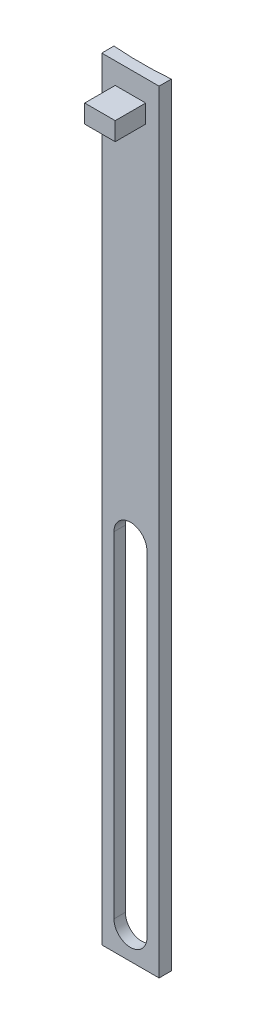
SolidWorks part; units mm, degrees
ref_plane "Front Plane" through (0, 0, 0) normal (0, 0, 1) x (1, 0, 0)
ref_plane "Top Plane" through (0, 0, 0) normal (0, 1, 0) x (1, 0, 0)
ref_plane "Right Plane" through (0, 0, 0) normal (1, 0, 0) x (0, 0, -1)
sketch "Sketch1" plane through (0, 0, 0) normal (0, 0, 1) x (1, 0, 0)
  line L0 (-2.7, -32.5) -> (-2.7, -87.5)
  line L1 (2.7, 32.5) -> (-2.7, 32.5)
  line L2 (2.7, 32.5) -> (2.7, -32.5)
  line L4 (-2.7, 32.5) -> (-2.7, -32.5)
  line L5 (2.7, 32.5) -> (-2.7, -32.5) construction
  line L6 (2.7, -32.5) -> (-2.7, 32.5) construction
  line L7 (-4.7, -32.5) -> (-4.7, 34.5)
  line L8 (-4.7, 34.5) -> (4.7, 34.5)
  line L9 (4.7, 34.5) -> (4.7, -32.5)
  line L10 (2.7, -87.5) -> (2.7, -32.5)
  line L11 (0, 29.2386) -> (0, -29.2386) construction
  line L12 (-4.7, -32.5) -> (-4.7, -92.2)
  line L13 (-4.7, -92.2) -> (4.7, -92.2)
  line L14 (4.7, -32.5) -> (4.7, -92.2)
  arc A2 (-2.7, -32.5) -> (2.7, -32.5) centre (0, -32.5) cw
  arc A3 (-2.7, -87.5) -> (2.7, -87.5) centre (0, -87.5) ccw
  point P0 (0, 0)
  point P13 (0, 0)
  point P19 (-2.7, -53.2591)
  point P20 (0, -90.2)
  dimension "D1" = 2.7
  dimension "D6" = 2
  dimension "D3" = 2
  dimension "D2" = 65
  dimension "D4" = 2
  dimension "D5" = 55
extrude "Boss-Extrude1" add sketch "Sketch1" along normal mid plane 2
sketch "Sketch2" plane through (0, 0, 0) normal (0, 1, 0) x (1, 0, 0)
  line L4 (4.7, 1) -> (-4.7, 1)
  line L5 (-4.7, 1) -> (-4.7, -1)
  line L6 (-4.7, -1) -> (4.7, -1)
  line L7 (4.7, -1) -> (4.7, 1)
  line L8 (4.7, 1) -> (-4.7, 1)
  line L9 (-4.7, 1) -> (-4.7, -1)
  line L10 (-4.7, -1) -> (4.7, -1)
  line L11 (4.7, -1) -> (4.7, 1)
  circle A0 centre (0, 57.8059) radius 57
  point P8 (0, 1)
  dimension "D2" = 114
  dimension "D1" = 0
extrude "Cut-Extrude2" cut sketch "Sketch2" against normal through all both and the other way through all contours L8 A0
sketch "Sketch3" plane through (0, 0, 1) normal (0, 0, 1) x (1, 0, 0)
  line L1 (-2.5, 31) -> (2.5, 31)
  line L2 (-2.5, 31) -> (-2.5, 28)
  line L3 (-2.5, 28) -> (2.5, 28)
  line L4 (2.5, 31) -> (2.5, 28)
  line L5 (-4.7, -92.2) -> (4.7, -92.2)
  line L6 (-4.7, -92.2) -> (4.7, -92.2)
  line L7 (4.7, -92.2) -> (4.7, 34.5)
  line L8 (4.7, 34.5) -> (-4.7, 34.5)
  line L9 (-4.7, 34.5) -> (-4.7, -92.2)
  line L12 (4.7, -92.2) -> (4.7, 34.5)
  line L13 (4.7, 34.5) -> (-4.7, 34.5)
  line L14 (-4.7, 34.5) -> (-4.7, -92.2)
  line L15 (-2.5, 31) -> (2.5, 28) construction
  line L16 (-2.5, 28) -> (2.5, 31) construction
  point P2 (0, 29.5)
  point P12 (0, 34.5)
  dimension "D2" = 5
  dimension "D3" = 5
  dimension "D4" = 3
  dimension "D1" = 0
extrude "Boss-Extrude2" add sketch "Sketch3" along normal blind 5 contours L2 L1 L4 L3
